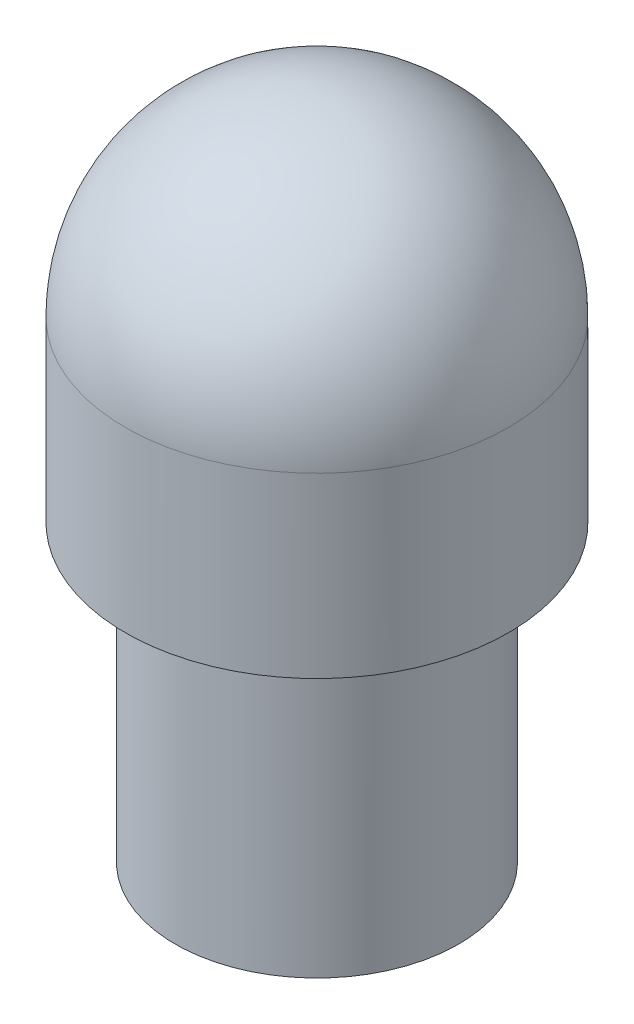
SolidWorks part; units mm, degrees
material "6061-T6 (SS)"
ref_plane "Front Plane" through (0, 0, 0) normal (0, 0, 1) x (1, 0, 0)
ref_plane "Top Plane" through (0, 0, 0) normal (0, 1, 0) x (1, 0, 0)
ref_plane "Right Plane" through (0, 0, 0) normal (1, 0, 0) x (0, 0, -1)
sketch "Sketch1" plane through (0, 0, 0) normal (0, 0, 1) x (1, 0, 0)
  line L0 (0, 25.4) -> (0, 43.6626) construction
  line L2 (4.8966, 14.7066) -> (-5.3865, 14.7066) construction
  line L3 (-5.2705, 38.3921) -> (-5.2705, 33.5026)
  line L4 (-5.2705, 33.5026) -> (-3.899, 33.5026)
  line L5 (-3.899, 33.5026) -> (-3.899, 25.4)
  line L6 (-3.899, 25.4) -> (0, 25.4)
  line L7 (0, 25.4) -> (0, 43.6626)
  arc A0 (0, 43.6626) -> (-5.2705, 38.3921) centre (0, 38.3921) ccw
  dimension "D2" = 10.541
  dimension "D1" = 28.956
  dimension "D3" = 7.798
  dimension "D4" = 18.2626
  dimension "D5" = 10.16
revolve "Revolve1" add sketch "Sketch1" angle 360 about L0
hole_wizard "M7x1.0 Tapped Hole1" positions "Sketch2" profile "Sketch3" tap size "M7x1.0" standard "ANSI Metric"
sketch "Sketch2" plane through (0, 25.4, 0) normal (0, -1, 0) x (-1, 0, 0)
  point P0 (0, 0)
sketch "Sketch3" plane through (0, 25.4, 0) normal (1, 0, 0) x (0, 0, -1)
  line L0 (0, 0) -> (0, 17.8046)
  line L1 (0, 17.8046) -> (3, 16.002)
  line L2 (3, 16.002) -> (3, 0)
  line L5 (3, 0) -> (0, 0)
  line L10 (0, 17.8046) -> (-3, 16.002) construction
  line L11 (0, -6.35) -> (0, 107.95) construction
  dimension "Tap Drill Dia." = 6
  dimension "Tap Drill Depth" = 16.002
  dimension "Drill Angle" = 118
cosmetic thread "Hole Thread1"
sketch "Sketch4" plane through (0, 25.4, 0) normal (0, -1, 0) x (1, 0, 0)
  circle A0 centre (0, 0) radius 3.5
  dimension "D1" = 7
extrude "Cut-Extrude1" cut sketch "Sketch4" against normal blind 2.5
fillet "Fillet1" radius 0.762 1 edges at (0, 33.5026, -3.899)
